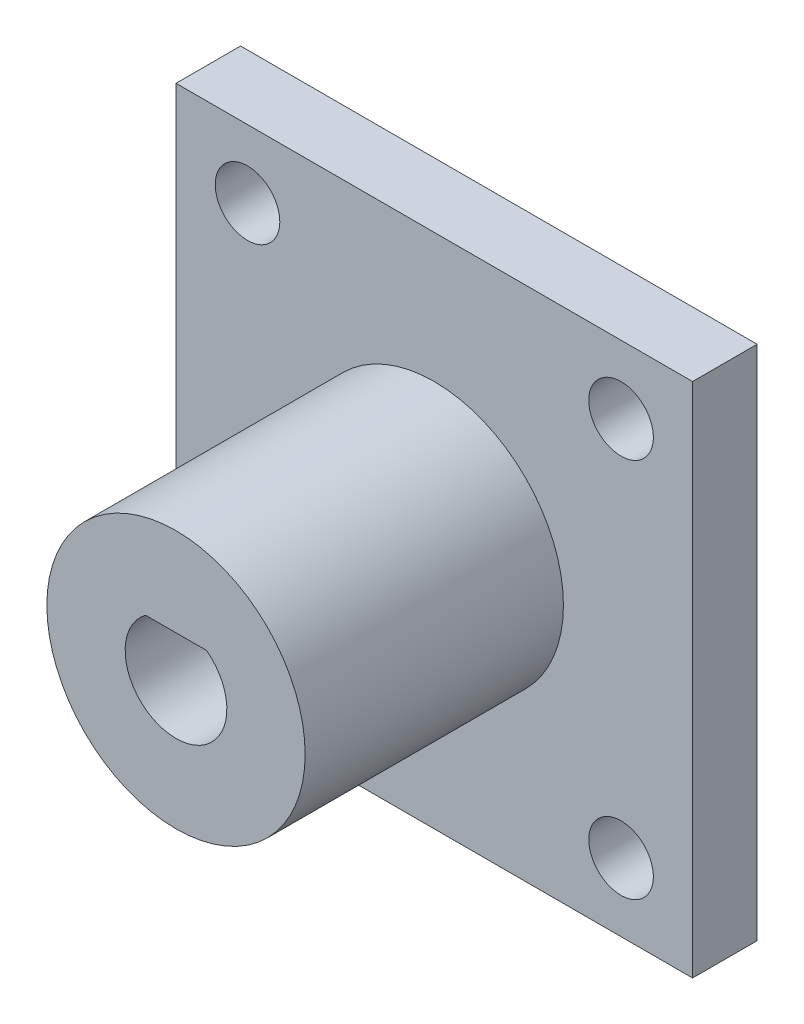
SolidWorks part; units mm, degrees
ref_plane "Front Plane" through (0, 0, 0) normal (0, 0, 1) x (1, 0, 0)
ref_plane "Top Plane" through (0, 0, 0) normal (0, 1, 0) x (1, 0, 0)
ref_plane "Right Plane" through (0, 0, 0) normal (1, 0, 0) x (0, 0, -1)
sketch "Sketch1" plane through (0, 0, 0) normal (0, 0, 1) x (1, 0, 0)
  line L5 (-3, 4) -> (3, 4)
  circle A0 centre (0, 0) radius 12.7
  arc A1 (-3, 4) -> (3, 4) centre (0, 0) ccw
  point P3 (0, 0)
  dimension "D1" = 10
  dimension "D2" = 25.4
  dimension "D3" = 4
extrude "Boss-Extrude5" add sketch "Sketch1" along normal blind 31.75
sketch "Sketch3" plane through (0, 0, 0) normal (0, 0, 1) x (1, 0, 0)
  line L1 (-25.4, -25.4) -> (25.4, -25.4)
  line L2 (-25.4, -25.4) -> (-25.4, 25.4)
  line L3 (-25.4, 25.4) -> (25.4, 25.4)
  line L4 (25.4, -25.4) -> (25.4, 25.4)
  line L5 (-25.4, -25.4) -> (25.4, 25.4) construction
  line L6 (-25.4, 25.4) -> (25.4, -25.4) construction
  point P0 (0, 0)
  dimension "D1" = 25.4
  dimension "D2" = 25.4
extrude "Boss-Extrude6" add sketch "Sketch3" along normal blind 6.35 separate body
sketch "Sketch4" plane through (0, 0, 0) normal (0, 0, -1) x (-1, 0, 0)
  line L0 (-25.4, 25.4) -> (25.4, 25.4) construction
  line L1 (-25.4, -25.4) -> (-25.4, 25.4) construction
  circle A0 centre (-18.3669, 18.7048) radius 3.175
  dimension "D1" = 6.6952
  dimension "D2" = 7.0331
  dimension "D3" = 6.35
extrude "Cut-Extrude1" cut sketch "Sketch4" against normal through all
mirror "Mirror1" about plane through (0, 0, 0) normal (1, 0, 0) of "Cut-Extrude1"
mirror "Mirror2" about plane through (0, 0, 0) normal (0, 1, 0) of "Mirror1", "Cut-Extrude1"
